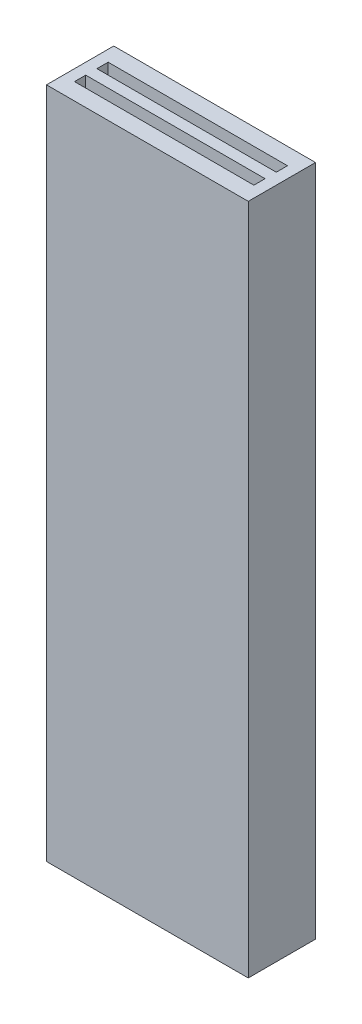
SolidWorks part; units mm, degrees
ref_plane "Front Plane" through (0, 0, 0) normal (0, 0, 1) x (1, 0, 0)
ref_plane "Top Plane" through (0, 0, 0) normal (0, 1, 0) x (1, 0, 0)
ref_plane "Right Plane" through (0, 0, 0) normal (1, 0, 0) x (0, 0, -1)
sketch "Sketch1" plane through (0, 0, 0) normal (0, 1, 0) x (1, 0, 0)
  line L1 (-4.5, -1.5) -> (4.5, -1.5)
  line L2 (-4.5, -1.5) -> (-4.5, 1.5)
  line L3 (-4.5, 1.5) -> (4.5, 1.5)
  line L4 (4.5, -1.5) -> (4.5, 1.5)
  line L5 (-4.5, -1.5) -> (4.5, 1.5) construction
  line L6 (-4.5, 1.5) -> (4.5, -1.5) construction
  point P0 (0, 0)
  dimension "D1" = 9
  dimension "D2" = 3
extrude "Boss-Extrude1" add sketch "Sketch1" along normal mid plane 30
sketch "Sketch2" plane through (0, 15, 0) normal (0, 1, 0) x (1, 0, 0)
  line L1 (-4, 0.25) -> (4, 0.25)
  line L2 (-4, 0.25) -> (-4, 0.75)
  line L3 (-4, 0.75) -> (4, 0.75)
  line L4 (4, 0.25) -> (4, 0.75)
  line L5 (-4, 0.25) -> (4, 0.75) construction
  line L6 (-4, 0.75) -> (4, 0.25) construction
  point P0 (0, 0.5)
  dimension "D1" = 0.5
  dimension "D2" = 8
  dimension "D3" = 0
  dimension "D4" = 0.5
extrude "Cut-Extrude1" cut sketch "Sketch2" against normal through all and the other way through all
mirror "Mirror1" about plane through (0, 0, 0) normal (0, 0, 1) of "Cut-Extrude1"
